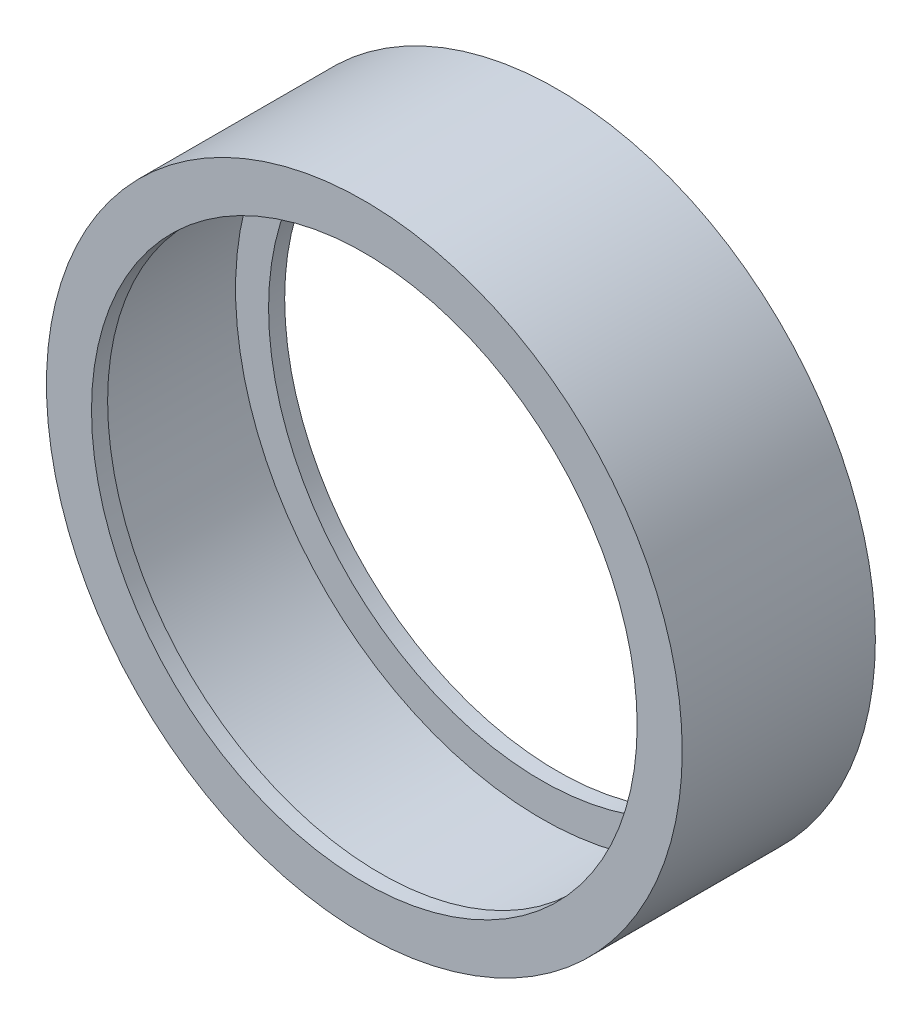
SolidWorks part; units mm, degrees
material "Rubber"
ref_plane "Front Plane" through (0, 0, 0) normal (0, 0, 1) x (1, 0, 0)
ref_plane "Top Plane" through (0, 0, 0) normal (0, 1, 0) x (1, 0, 0)
ref_plane "Right Plane" through (0, 0, 0) normal (1, 0, 0) x (0, 0, -1)
sketch "Sketch2" plane through (0, 0, 0) normal (0, 0, 1) x (1, 0, 0)
  circle A0 centre (0, 0) radius 8.6106
extrude "Boss-Extrude1" add sketch "Sketch2" against normal blind 4.064
sketch "Sketch3" plane through (0, 0, 0) normal (0, 0, 1) x (1, 0, 0)
  line L0 (0, 8.6106) -> (0, 10.033) construction
  circle A0 centre (0, 0) radius 8.6106 construction
  circle A1 centre (0, 0) radius 10.033
extrude "Boss-Extrude2" add sketch "Sketch3" against normal blind 5.08
sketch "Sketch4" plane through (0, 0, 0) normal (0, 0, 1) x (1, 0, 0)
  circle A0 centre (0, 0) radius 8.6106
extrude "Cut-Extrude1" cut sketch "Sketch4" against normal through all
sketch "Sketch9" plane through (0, 0, 0) normal (0, 0, 1) x (1, 0, 0)
  circle A0 centre (0, 0) radius 10.033
  circle A1 centre (0, 0) radius 8.128
extrude "Boss-Extrude3" add sketch "Sketch9" along normal blind 0.508
sketch "Sketch10" plane through (0, 0, -5.08) normal (0, 0, -1) x (-1, 0, 0)
  circle A0 centre (0, 0) radius 8.128
  circle A1 centre (0, 0) radius 10.033
extrude "Boss-Extrude4" add sketch "Sketch10" along normal blind 0.508
sketch "Sketch12" plane through (0, 0, -5.588) normal (0, 0, -1) x (-1, 0, 0)
  circle A0 centre (0, 0) radius 9.271
extrude "Cut-Extrude2" cut sketch "Sketch12" against normal through all
sketch "Sketch13" plane through (0, 0, -5.588) normal (0, 0, -1) x (-1, 0, 0)
  circle A0 centre (0, 0) radius 10.033
  circle A1 centre (0, 0) radius 9.271
extrude "Cut-Extrude3" cut sketch "Sketch13" against normal blind 0.508 contours A0
sketch "Sketch15" plane through (0, 0, 0.508) normal (0, 0, 1) x (1, 0, 0)
  circle A0 centre (0, 0) radius 9.271
  circle A1 centre (0, 0) radius 10.033
extrude "Cut-Extrude4" cut sketch "Sketch15" against normal blind 0.508
sketch "Sketch16" plane through (0, 0, 0) normal (0, 0, 1) x (1, 0, 0)
  circle A0 centre (0, 0) radius 9.652
  circle A1 centre (0, 0) radius 9.271
extrude "Cut-Extrude5" cut sketch "Sketch16" against normal through all
sketch "Sketch17" plane through (0, 0, 0) normal (0, 0, 1) x (1, 0, 0)
  circle A0 centre (0, 0) radius 8.6106
  circle A1 centre (0, 0) radius 10.033
extrude "Boss-Extrude5" add sketch "Sketch17" along normal blind 0.508
sketch "Sketch18" plane through (0, 0, -5.08) normal (0, 0, -1) x (-1, 0, 0)
  circle A0 centre (0, 0) radius 8.6106
  circle A1 centre (0, 0) radius 10.033
extrude "Boss-Extrude6" add sketch "Sketch18" along normal blind 0.508
scale "Scale1" scale about centroid uniform scaling yes scale factor 0.5
